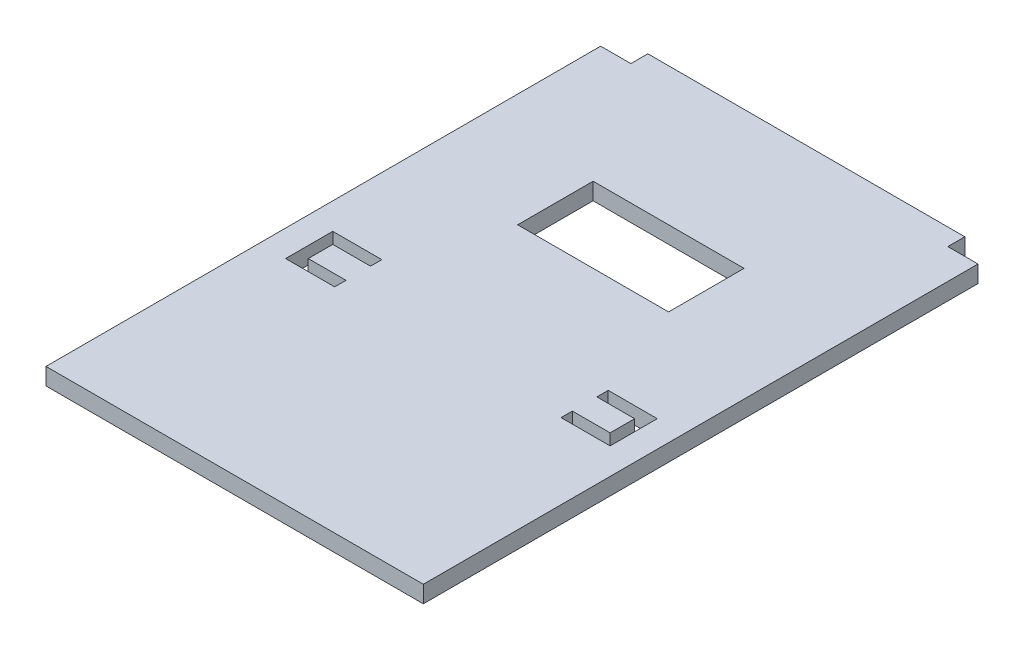
SolidWorks part; units mm, degrees
material "Teak"
ref_plane "Front Plane" through (0, 0, 0) normal (0, 0, 1) x (1, 0, 0)
ref_plane "Top Plane" through (0, 0, 0) normal (0, 1, 0) x (1, 0, 0)
ref_plane "Right Plane" through (0, 0, 0) normal (1, 0, 0) x (0, 0, -1)
sketch "Sketch1" plane through (0, 0, 0) normal (0, 1, 0) x (1, 0, 0)
  line L0 (50, 73.5) -> (42, 73.5) construction
  line L1 (50, 73.5) -> (50, -73.5) construction
  line L2 (50, -73.5) -> (-50, -73.5) construction
  line L3 (-50, -73.5) -> (-50, 73.5) construction
  line L4 (-42, 73.5) -> (-50, 73.5) construction
  line L5 (30, -17) -> (43, -17) construction
  line L6 (-30, -17) -> (-40, -17) construction
  line L7 (-42, 73.5) -> (-42, 78) construction
  line L8 (-42, 78) -> (42, 78) construction
  line L9 (42, 73.5) -> (42, 78) construction
  line L10 (-40, -4.5) -> (-30, -4.5) construction
  line L11 (30, -17) -> (30, -14) construction
  line L12 (30, -7.5) -> (30, -4.5) construction
  line L13 (30, -4.5) -> (43, -4.5) construction
  line L14 (-40, -4.5) -> (-43, -4.5) construction
  line L15 (-43, -4.5) -> (-43, -17) construction
  line L16 (-43, -17) -> (-40, -17) construction
  line L17 (43, -4.5) -> (43, -17) construction
  line L18 (-20, 21.5) -> (-20, 41.5) construction
  line L19 (-20, 41.5) -> (20, 41.5) construction
  line L20 (20, 41.5) -> (20, 21.5) construction
  line L21 (20, 21.5) -> (-20, 21.5) construction
  line L22 (-30, -7.5) -> (-40, -7.5) construction
  line L23 (-40, -7.5) -> (-40, -14) construction
  line L24 (-40, -14) -> (-30, -14) construction
  line L25 (-30, -4.5) -> (-30, -7.5) construction
  line L26 (-30, -14) -> (-30, -17) construction
  line L27 (30, -7.5) -> (40, -7.5) construction
  line L28 (40, -7.5) -> (40, -14) construction
  line L29 (40, -14) -> (30, -14) construction
sketch "Sketch2" plane through (0, 0, 0) normal (0, 1, 0) x (1, 0, 0)
  line L0 (-42, 73.5) -> (-42, 78) construction
  line L1 (-42, 73.5) -> (-42, 78)
  line L2 (-42, 78) -> (42, 78) construction
  line L3 (-42, 78) -> (42, 78)
  line L4 (-43, -4.5) -> (-43, -17) construction
  line L5 (-30, -14) -> (-30, -17) construction
  line L6 (-30, -4.5) -> (-30, -7.5) construction
  line L7 (-40, -7.5) -> (-40, -14) construction
  line L8 (-30, -7.5) -> (-40, -7.5) construction
  line L9 (-40, -14) -> (-30, -14) construction
  line L10 (30, -17) -> (30, -14) construction
  line L11 (30, -17) -> (43, -17) construction
  line L12 (43, -4.5) -> (43, -17) construction
  line L13 (20, 41.5) -> (20, 21.5) construction
  line L14 (-20, 21.5) -> (-20, 41.5) construction
  line L15 (-20, 41.5) -> (20, 41.5) construction
  line L16 (20, 21.5) -> (-20, 21.5) construction
  line L17 (30, -7.5) -> (30, -4.5) construction
  line L18 (30, -4.5) -> (43, -4.5) construction
  line L19 (40, -7.5) -> (40, -14) construction
  line L20 (30, -7.5) -> (40, -7.5) construction
  line L21 (40, -14) -> (30, -14) construction
  line L22 (50, -73.5) -> (-50, -73.5) construction
  line L23 (50, 73.5) -> (50, -73.5) construction
  line L24 (42, 73.5) -> (42, 78) construction
  line L25 (50, 73.5) -> (42, 73.5) construction
  line L26 (-50, -73.5) -> (-50, 73.5) construction
  line L27 (-42, 73.5) -> (-50, 73.5) construction
  line L28 (-43, -4.5) -> (-43, -17)
  line L29 (-30, -14) -> (-30, -17)
  line L30 (-30, -4.5) -> (-30, -7.5)
  line L31 (-40, -7.5) -> (-40, -14)
  line L32 (-30, -7.5) -> (-40, -7.5)
  line L33 (-40, -14) -> (-30, -14)
  line L34 (30, -17) -> (30, -14)
  line L35 (30, -17) -> (43, -17)
  line L36 (43, -4.5) -> (43, -17)
  line L37 (20, 41.5) -> (20, 21.5)
  line L38 (-20, 21.5) -> (-20, 41.5)
  line L39 (-20, 41.5) -> (20, 41.5)
  line L40 (20, 21.5) -> (-20, 21.5)
  line L41 (30, -7.5) -> (30, -4.5)
  line L42 (30, -4.5) -> (43, -4.5)
  line L43 (40, -7.5) -> (40, -14)
  line L44 (30, -7.5) -> (40, -7.5)
  line L45 (40, -14) -> (30, -14)
  line L46 (50, -73.5) -> (-50, -73.5)
  line L47 (50, 73.5) -> (50, -73.5)
  line L48 (42, 73.5) -> (42, 78)
  line L49 (50, 73.5) -> (42, 73.5)
  line L50 (-50, -73.5) -> (-50, 73.5)
  line L51 (-42, 73.5) -> (-50, 73.5)
  line L52 (-43, -4.5) -> (-30, -4.5)
  line L53 (-43, -17) -> (-30, -17)
extrude "Boss-Extrude1" add sketch "Sketch2" along normal blind 4.5
